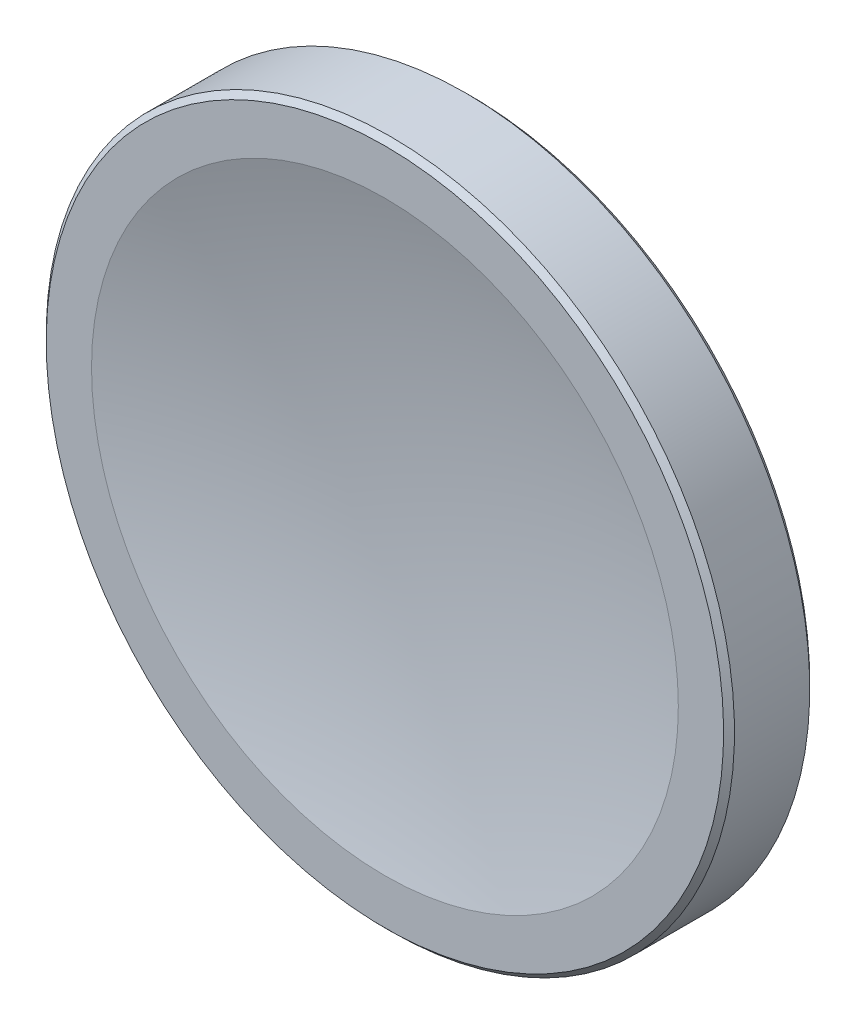
SolidWorks part; units mm, degrees
material "Silica"
ref_plane "Front" through (0, 0, 0) normal (0, 0, 1) x (1, 0, 0)
ref_plane "Top" through (0, 0, 0) normal (0, 1, 0) x (1, 0, 0)
ref_plane "Right" through (0, 0, 0) normal (1, 0, 0) x (0, 0, -1)
sketch "Sketch1" plane through (0, 0, 0) normal (1, 0, 0) x (0, 0, -1)
  line L0 (-662.018, 0) -> (662.018, 0) construction
  line L1 (-458.4143, 54) -> (-458.4143, 63.3349)
  line L2 (-458.4143, 63.3349) -> (-442.5558, 63.3349)
  line L3 (-442.5558, 63.3349) -> (-442.5558, 54)
  line L4 (-451.375, 0) -> (-443.875, 0)
  arc A0 (-458.4143, 54) -> (-451.375, 0) centre (-662.018, 0) cw
  arc A1 (-443.875, 0) -> (-442.5558, 54) centre (662.018, 0) cw
  point P3 (0, 0)
revolve "Revolve3" add sketch "Sketch1" angle 360 about L0
chamfer "Chamfer1" distance 1 angle 45 2 edges at (0, -63.3349, 442.5558) (0, -63.3349, 458.4143)
ref_plane "Plane1" through (0, 0, 443.875) normal (0, 0, -1) x (-1, 0, 0)
equation "\"D3@Sketch1\"=210.643+7.5+1105.893"
equation "\"D6@Sketch1\"=4.987*25.4/2"
